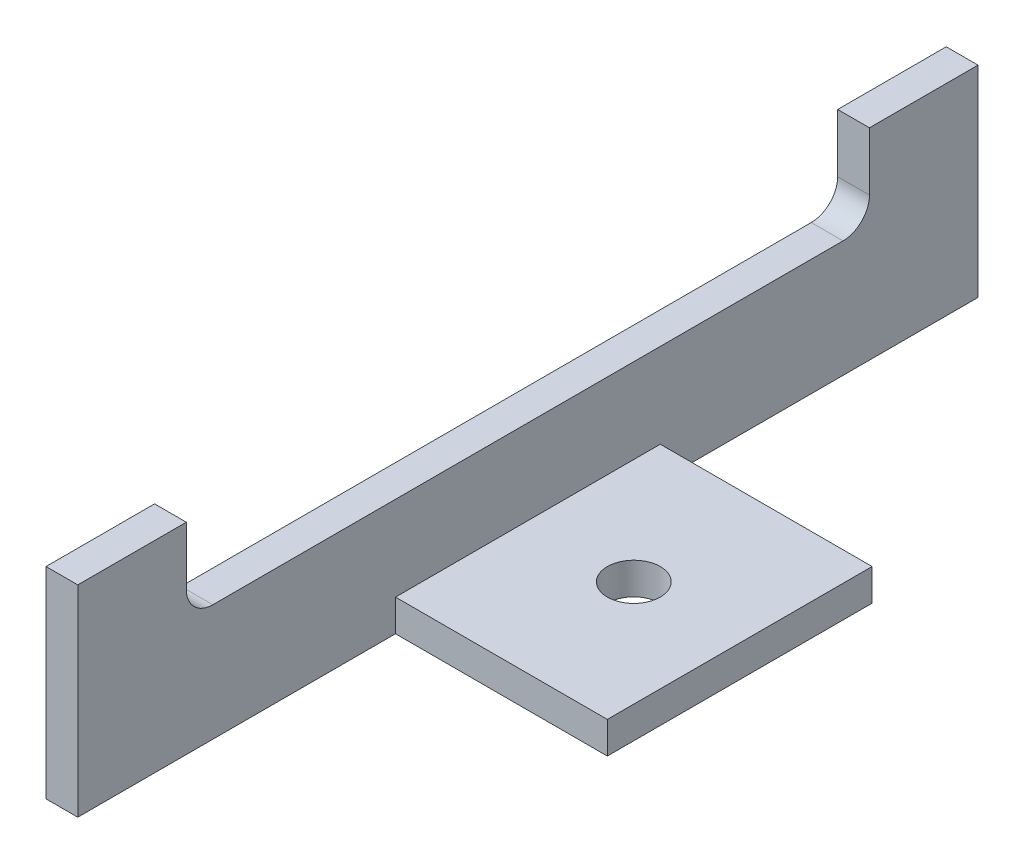
SolidWorks part; units mm, degrees
material "1060-H16"
ref_plane "Alzado" through (0, 0, 0) normal (0, 0, 1) x (1, 0, 0)
ref_plane "Planta" through (0, 0, 0) normal (0, 1, 0) x (1, 0, 0)
ref_plane "Vista lateral" through (0, 0, 0) normal (1, 0, 0) x (0, 0, -1)
sketch "Croquis1" plane through (0, 0, 0) normal (0, 0, 1) x (1, 0, 0)
  line L0 (0, 0) -> (0, 50)
  line L1 (0, 0) -> (50, 0)
  line L2 (6, 6) -> (50, 6)
  line L3 (6, 6) -> (6, 50)
  line L4 (0, 50) -> (6, 50)
  line L5 (50, 6) -> (50, 0)
  dimension "D2" = 50
  dimension "D1" = 6
extrude "Saliente-Extruir1" add sketch "Croquis1" along normal blind 170
sketch "Croquis2" plane through (0, 0, 0) normal (-1, 0, 0) x (0, 0, 1)
  line L0 (170, 35) -> (0, 35) construction
  line L1 (170, 50) -> (170, 0) construction
  line L2 (0, 50) -> (0, 0) construction
  line L3 (170, 6) -> (0, 6) construction
  line L4 (170, 6) -> (0, 6) construction
  line L5 (85, 6) -> (85, 50) construction
  line L6 (170, 50) -> (0, 50) construction
  line L7 (112.5, 22) -> (112.5, 50)
  line L8 (112.5, 78) -> (57.5, 78) construction
  line L9 (112.5, 78) -> (112.5, 22) construction
  line L10 (112.5, 22) -> (57.5, 22)
  line L11 (57.5, 78) -> (57.5, 22) construction
  line L12 (112.5, 78) -> (57.5, 22) construction
  line L13 (112.5, 22) -> (57.5, 78) construction
  line L14 (57.5, 22) -> (57.5, 50)
  line L15 (57.5, 50) -> (112.5, 50)
  line L16 (149.5, 35) -> (149.5, 50)
  line L17 (130.5, 35) -> (130.5, 50)
  line L18 (130.5, 50) -> (149.5, 50)
  line L19 (39.5, 35) -> (39.5, 50)
  line L20 (20.5, 35) -> (20.5, 50)
  line L21 (39.5, 50) -> (20.5, 50)
  line L22 (170, 0) -> (0, 0) construction
  circle A0 centre (140, 35) radius 9.5 construction
  circle A1 centre (30, 35) radius 9.5 construction
  arc A2 (149.5, 35) -> (130.5, 35) centre (140, 35) cw
  arc A3 (39.5, 35) -> (20.5, 35) centre (30, 35) cw
  dimension "D2" = 19
  dimension "D1" = 35
  dimension "D3" = 55
  dimension "D4" = 55
  dimension "D5" = 22
  dimension "D6" = 55
  dimension "D7" = 20.5
  dimension "D8" = 20.5
extrude "Cortar-Extruir1" cut sketch "Croquis2" against normal up to surface (6 mm away) up to face at (6, 28, 85)
sketch "Croquis3" plane through (0, 0, 0) normal (0, -1, 0) x (1, 0, 0)
  line L0 (0, 85) -> (50, 85) construction
  line L1 (0, 170) -> (0, 0) construction
  line L2 (50, 170) -> (50, 0) construction
  line L3 (6, 170) -> (6, 0) construction
  line L4 (50, 0) -> (6, 0)
  line L5 (50, 0) -> (50, 60)
  line L6 (50, 60) -> (6, 60)
  line L7 (6, 0) -> (6, 60)
  line L8 (6, 170) -> (6, 0) construction
  line L9 (50, 110) -> (6, 110)
  line L10 (6, 170) -> (6, 110)
  line L11 (50, 170) -> (6, 170)
  line L12 (50, 170) -> (50, 110)
  line M5 (0, 0) -> (50, 0)
  line M6 (50, 0) -> (50, 170)
  line M7 (50, 170) -> (0, 170)
  dimension "D1" = 60
extrude "Cortar-Extruir2" cut sketch "Croquis3" against normal up to surface (6 mm away) contours L10 L9 M7 M6 | L7 L6 M5 M6 up to face at (28, 6, 85)
sketch "Croquis4" plane through (0, 0, 0) normal (0, -1, 0) x (1, 0, 0)
  line L0 (46, 60) -> (46, 110)
  line L1 (50, 60) -> (6, 60) construction
  line L2 (50, 110) -> (6, 110) construction
  line L3 (46, 110) -> (50, 110)
  line L4 (50, 110) -> (50, 60)
  line L5 (50, 60) -> (46, 60)
  dimension "D1" = 4
extrude "Cortar-Extruir3" cut sketch "Croquis4" against normal blind 10
sketch "Croquis5" plane through (0, 0, 0) normal (-1, 0, 0) x (0, 0, 1)
  line L0 (170, 38) -> (0, 38) construction
  line L1 (170, 50) -> (170, 0) construction
  line L2 (0, 50) -> (0, 0) construction
  line L3 (170, 50) -> (149.5, 50) construction
  line L4 (170, 38) -> (149.5, 38)
  line L5 (149.5, 38) -> (149.5, 50)
  line L6 (149.5, 50) -> (170, 50)
  line L7 (170, 50) -> (170, 38)
  line L8 (149.5, 35) -> (149.5, 50) construction
  line L9 (112.5, 50) -> (112.5, 38)
  line L10 (112.5, 22) -> (112.5, 50) construction
  line L11 (112.5, 38) -> (130.5, 38)
  line L12 (130.5, 50) -> (130.5, 35) construction
  line L13 (130.5, 38) -> (130.5, 50)
  line L14 (130.5, 50) -> (112.5, 50)
  line L15 (85, 22) -> (85, 38) construction
  line L16 (57.5, 22) -> (112.5, 22) construction
  line L17 (39.5, 38) -> (39.5, 50)
  line L18 (57.5, 38) -> (39.5, 38)
  line L19 (57.5, 50) -> (57.5, 38)
  line L20 (39.5, 50) -> (57.5, 50)
  line L21 (20.5, 50) -> (0, 50)
  line L22 (20.5, 38) -> (20.5, 50)
  line L23 (0, 38) -> (20.5, 38)
  line L24 (0, 50) -> (0, 38)
  dimension "D1" = 12
extrude "Cortar-Extruir4" cut sketch "Croquis5" against normal up to surface (6 mm away) up to face at (6, 28.85, 85)
sketch "Croquis6" plane through (0, 0, 0) normal (-1, 0, 0) x (0, 0, 1)
  line L0 (149.5, 38) -> (149.5, 22)
  line L1 (149.5, 22) -> (20.5, 22)
  line L2 (20.5, 22) -> (20.5, 38)
  line L3 (170, 0) -> (0, 0) construction
  line L4 (149.5, 38) -> (20.5, 38)
  dimension "D1" = 22
extrude "Cortar-Extruir5" cut sketch "Croquis6" against normal up to surface (6 mm away) up to face at (6, 24.05, 85)
sketch "Croquis7" plane through (0, 0, 0) normal (0, -1, 0) x (1, 0, 0)
  circle A0 centre (26, 85) radius 5 construction
  circle A1 centre (26, 85) radius 5
extrude "Cortar-Extruir6" cut sketch "Croquis7" against normal up to surface (6 mm away) up to face at (26, 6, 85)
fillet "Redondeo1" radius 5 2 edges at (3, 22, 149.5) (3, 22, 20.5)
